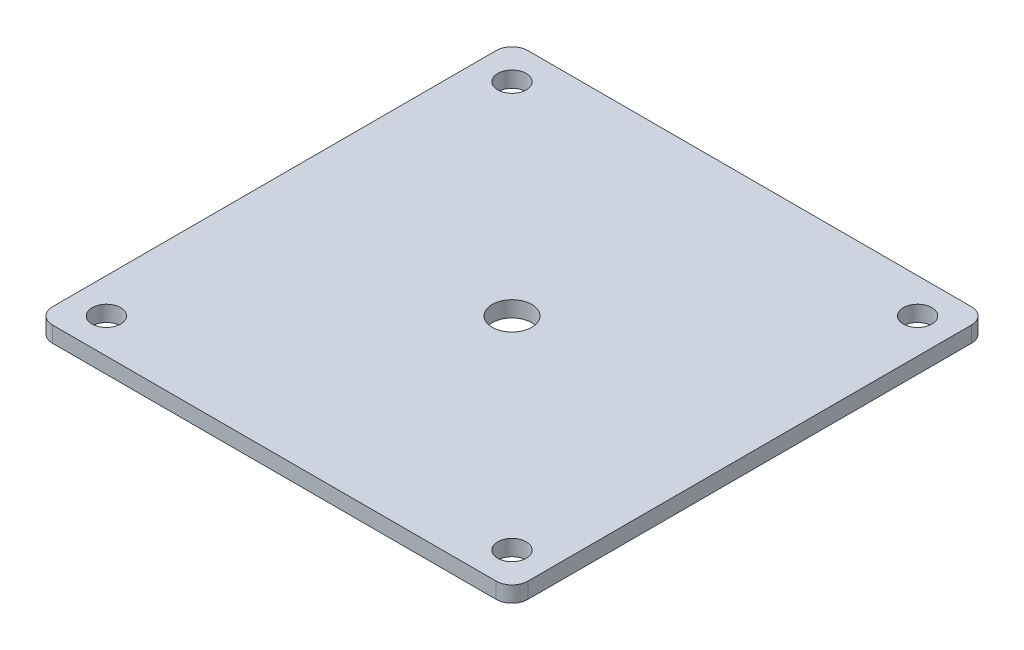
SolidWorks part; units mm, degrees
material "ABS"
ref_plane "Front Plane" through (0, 0, 0) normal (0, 0, 1) x (1, 0, 0)
ref_plane "Top Plane" through (0, 0, 0) normal (0, 1, 0) x (1, 0, 0)
ref_plane "Right Plane" through (0, 0, 0) normal (1, 0, 0) x (0, 0, -1)
sketch "Sketch2" plane through (0, 0, 0) normal (0, 1, 0) x (1, 0, 0)
  line L1 (-38.1, 38.1) -> (38.1, 38.1)
  line L2 (-38.1, 38.1) -> (-38.1, -38.1)
  line L3 (-38.1, -38.1) -> (38.1, -38.1)
  line L4 (38.1, 38.1) -> (38.1, -38.1)
  line L5 (-38.1, 38.1) -> (38.1, -38.1) construction
  line L6 (-38.1, -38.1) -> (38.1, 38.1) construction
  point P0 (0, 0)
  dimension "D1" = 76.2
  dimension "D2" = 76.2
extrude "Boss-Extrude2" add sketch "Sketch2" along normal blind 2.54
sketch "Sketch5" plane through (0, 2.54, 0) normal (0, 1, 0) x (1, 0, 0)
  circle A0 centre (-32.512, 32.512) radius 2.286
  circle A1 centre (32.512, 32.512) radius 2.286
  circle A2 centre (32.512, -32.512) radius 2.286
  circle A3 centre (-32.512, -32.512) radius 2.286
  dimension "D1" = 4.572
  dimension "D2" = 4.572
  dimension "D3" = 4.572
  dimension "D4" = 4.572
  dimension "D5" = 65.024
  dimension "D6" = 65.024
  dimension "D7" = 65.024
  dimension "D8" = 32.512
  dimension "D9" = 32.512
  dimension "D10" = 32.512
  dimension "D11" = 32.512
extrude "Cut-Extrude1" cut sketch "Sketch5" against normal blind 2.54
sketch "Sketch6" plane through (0, 2.54, 0) normal (0, 1, 0) x (1, 0, 0)
  circle A0 centre (0, 0) radius 3.175
  dimension "D1" = 6.35
extrude "Cut-Extrude2" cut sketch "Sketch6" against normal blind 2.54
fillet "Fillet3" radius 2.54 4 edges at (-38.1, 1.27, 38.1) (38.1, 1.27, 38.1) (38.1, 1.27, -38.1) (-38.1, 1.27, -38.1)
